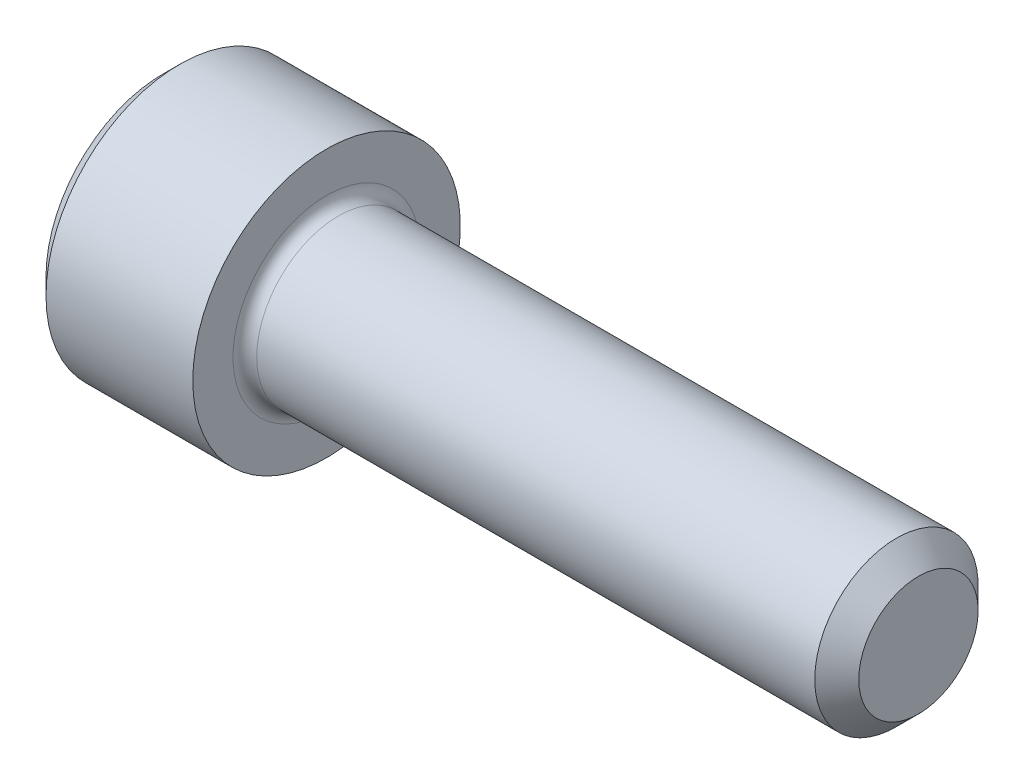
SolidWorks part; units mm, degrees
ref_plane "Plane1" through (0, 0, 0) normal (0, 0, 1) x (1, 0, 0)
ref_plane "Plane2" through (0, 0, 0) normal (0, 1, 0) x (1, 0, 0)
ref_plane "Plane3" through (0, 0, 0) normal (1, 0, 0) x (0, 0, -1)
sketch "BodySke" plane through (0, 0, 0) normal (0, 0, 1) x (1, 0, 0)
  line L0 (0, 0) -> (0, 2.5146)
  line L1 (0.3556, 2.8702) -> (3.5052, 2.8702)
  line L2 (3.5052, 2.8702) -> (3.5052, 1.7526)
  line L3 (3.5052, 1.7526) -> (15.7328, 1.7526)
  line L4 (16.2052, 1.2802) -> (16.2052, 0)
  line L5 (16.2052, 0) -> (0, 0)
  line L6 (-31.75, 0) -> (127, 0) construction
  line L7 (0, 2.5146) -> (0.3556, 2.8702)
  line L8 (16.2052, 1.2802) -> (15.7328, 1.7526)
  line L9 (0, -2.5146) -> (0.3556, -2.8702) construction
  line L10 (16.2052, -1.2802) -> (15.7328, -1.7526) construction
  line L11 (4.2977, 9.525) -> (4.2977, 3.175) construction
  line L12 (3.5052, 9.525) -> (3.5052, 3.175) construction
  line L13 (-21.8948, 9.525) -> (-21.8948, 3.175) construction
  dimension "Diameter" = 3.5052
  dimension "Head_ht" = 3.5052
  dimension "Length" = 12.7
  dimension "Body_ch_ang" = 45
  dimension "Head_dia" = 5.7404
  dimension "Head_ch_ang" = 45
  dimension "Head_side_ht" = 3.1496
  dimension "Minor_dia" = 2.5603
  dimension "Advance" = 0.7925
  dimension "Thread_nom" = 12.7
  dimension "Thread_length" = 38.1
revolve "Base-Revolve" add sketch "BodySke"
cosmetic thread "ThreadCosmetic" [suppressed]
fillet "Fillet1" radius 0.254 1 edges at (3.5052, 0, 1.7526)
sketch "Sketch2" plane through (0, 0, 0) normal (0, 0, 1) x (1, 0, 0)
  line L0 (0, 1.3843) -> (1.6256, 1.3843)
  line L1 (1.6256, 1.3843) -> (2.4248, 0)
  line L2 (-31.75, 0) -> (127, 0) construction
  line L3 (2.4248, 0) -> (0, 0)
  line L4 (0, 0) -> (0, 1.3843)
  line L5 (0, 2.5146) -> (0, -2.5146) construction
  line L6 (0, 0) -> (47.625, 0) construction
  line L7 (3.5052, -2.8702) -> (3.5052, 2.8702) construction
  dimension "D1" = 1.3843
  dimension "D2" = 60
  dimension "Wall_thickness" = 1.8796
revolve "Hex-PreBroach" cut sketch "Sketch2" angle 360 about L6
sketch "Sketch3" plane through (0, 0, 0) normal (-1, 0, 0) x (0, 0.5, 0.866)
  line L0 (0.7992, 1.3843) -> (-0.7992, 1.3843)
  line L1 (-0.7992, 1.3843) -> (-1.5985, 0)
  line L2 (0.7992, 1.3843) -> (1.5985, 0)
  line L3 (0.7992, -1.3843) -> (1.5985, 0)
  line L4 (0.7992, -1.3843) -> (-0.7992, -1.3843)
  line L5 (-0.7992, -1.3843) -> (-1.5985, 0)
  dimension "D1" = 1.3843
  dimension "D2" = 1.3843
  dimension "Hex_size" = 2.7686
extrude "Hex" cut sketch "Sketch3" against normal blind 1.6256
sketch "Sketch4" plane through (0, 0, 0) normal (-1, 0, 0) x (0, 0, 1)
  line L0 (0, 0) -> (1.7399, 0)
  line L1 (0, 0) -> (6.1484, 3.5498) construction
  line L2 (0, 0) -> (0.8699, 1.5068)
  line L3 (1.4457, 0.3947) -> (1.6607, 0.5189)
  line L4 (1.0647, 1.0546) -> (1.2797, 1.1788)
  arc A0 (1.4457, 0.3947) -> (1.0647, 1.0546) centre (0, 0) ccw
  arc A1 (1.7399, 0) -> (1.6607, 0.5189) centre (0, 0) ccw
  arc A2 (0.8699, 1.5068) -> (1.2797, 1.1788) centre (0, 0) cw
  dimension "D1" = 30
  dimension "Spline_n_dim" = 2.9972
  dimension "Spline_m_dim" = 3.4798
  dimension "D2" = 60
  dimension "D3" = 0.381
  dimension "Spline_p_dim" = 0.762
extrude "Spline" [suppressed] cut sketch "Sketch4" against normal blind 1.6256
pattern_circular "CirPattern1" [suppressed] count 6 every 60
sketch "Sketch5" plane through (0, 0, 0) normal (0, 0, 1) x (1, 0, 0)
  line L0 (-31.75, 0) -> (127, 0) construction
  line L2 (0, 2.5146) -> (0, -2.5146) construction
  circle A0 centre (1.27, 0) radius 0.4445
  dimension "Drilled_hole_dia" = 0.889
  dimension "Drilled_hole_loc" = 1.27
extrude "Hole" [suppressed] cut sketch "Sketch5" against normal through all and the other way through all
pattern_circular "Drilled-4" [suppressed] count 2 every 60
pattern_circular "Drilled-6" [suppressed] count 3 every 60
sketch "ThdSchSke" plane through (0, 0, 0) normal (0, 0, 1) x (1, 0, 0)
  line L0 (4.2977, -1.2802) -> (3.9669, -1.7526)
  line L1 (4.2977, -1.2802) -> (4.6285, -1.7526)
  line L2 (4.6285, -1.7526) -> (4.6285, -2.1907)
  line L3 (-3.175, 0) -> (5.1513, 0) construction
  line L5 (4.6285, -2.1907) -> (3.9669, -2.1907)
  line L6 (3.9669, -2.1907) -> (3.9669, -1.7526)
  line L7 (0, 2.5146) -> (0, -2.5146) construction
  dimension "Thread_minor" = 2.5603
  dimension "Diameter" = 3.5052
  dimension "Start" = 4.2977
  dimension "SideAngle" = 55
  dimension "VeeAngle" = 70
  dimension "Overcut" = 4.3815
revolve "ThreadSchematic" [suppressed] cut sketch "ThdSchSke" angle 360 about L3
pattern_linear "ThdSchPat" [suppressed]
equation "\"D2@Sketch3\" = \"Hex_size@Sketch3\" / 2"
equation "\"D1@Sketch3\" = \"Hex_size@Sketch3\" / 2"
equation "\"D1@Sketch2\" = \"Hex_size@Sketch3\" / 2"
equation "\"D3@Sketch4\" = \"Spline_p_dim@Sketch4\" / 2"
equation "\"Thread_minor@ThreadCosmetic\"  =  \"Minor_dia@BodySke\""
equation "\"D2@CirPattern1\" = 360 / \"Num_teeth@CirPattern1\""
equation "\"Wall_thickness@Sketch2\" = \"Head_ht@BodySke\" - \"Key_eng@Hex\""
equation "\"Thread_length@ThreadCosmetic\" = ((sgn( (\"Length@BodySke\" - \"Advance@BodySke\" ) - \"Thread_nom@BodySke\" )-1)*( (\"Length@BodySke\" - \"Advance@BodySke\" ) - \"Thread_nom@BodySke\" ))/-2+ \"Thread_nom@BodySke\""
equation "\"Thread_minor@ThdSchSke\" = \"Minor_dia@BodySke\""
equation "\"Diameter@ThdSchSke\" = \"Diameter@BodySke\""
equation "\"Overcut@ThdSchSke\" = \"Diameter@BodySke\" * 1.25"
equation "\"Start@ThdSchSke\" = \"Head_ht@BodySke\" + \"Length@BodySke\" - \"Thread_length@ThreadCosmetic\"  '---Non-countersunk---"
equation "\"Num_threads@ThdSchPat\" = int( \"Thread_length@ThreadCosmetic\" / \"Advance@BodySke\" + 0.999 )  + 1"
equation "\"Advance@ThdSchPat\" = \"Thread_length@ThreadCosmetic\" /  (\"Num_threads@ThdSchPat\" - 1) 'relax it"
equation "\"Num_threads@ThdSchPat\" = \"Num_threads@ThdSchPat\" - sgn( \"Num_threads@ThdSchPat\" - 1) '---chamfered tips only---"
